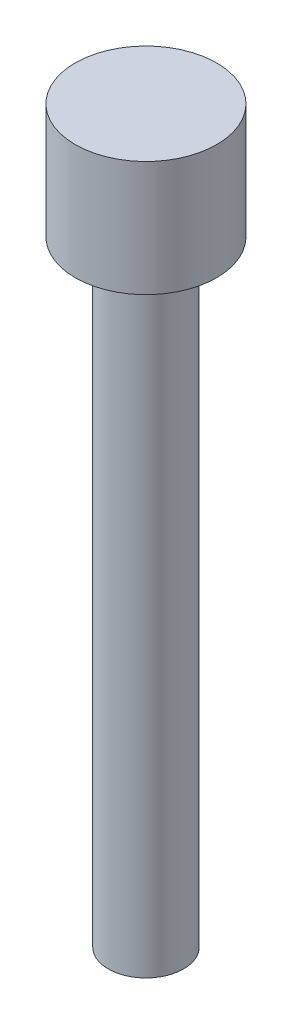
SolidWorks part; units mm, degrees
ref_plane "Front Plane" through (0, 0, 0) normal (0, 0, 1) x (1, 0, 0)
ref_plane "Top Plane" through (0, 0, 0) normal (0, 1, 0) x (1, 0, 0)
ref_plane "Right Plane" through (0, 0, 0) normal (1, 0, 0) x (0, 0, -1)
sketch "Sketch1" plane through (0, 0, 0) normal (0, 1, 0) x (1, 0, 0)
  circle A0 centre (0, 0) radius 1.84
  dimension "D1" = 3.68
extrude "Boss-Extrude1" add sketch "Sketch1" along normal blind 3
sketch "Sketch2" plane through (0, 0, 0) normal (0, -1, 0) x (1, 0, 0)
  circle A0 centre (0, 0) radius 0.98
  dimension "D1" = 1.96
extrude "Boss-Extrude2" add sketch "Sketch2" along normal blind 16
